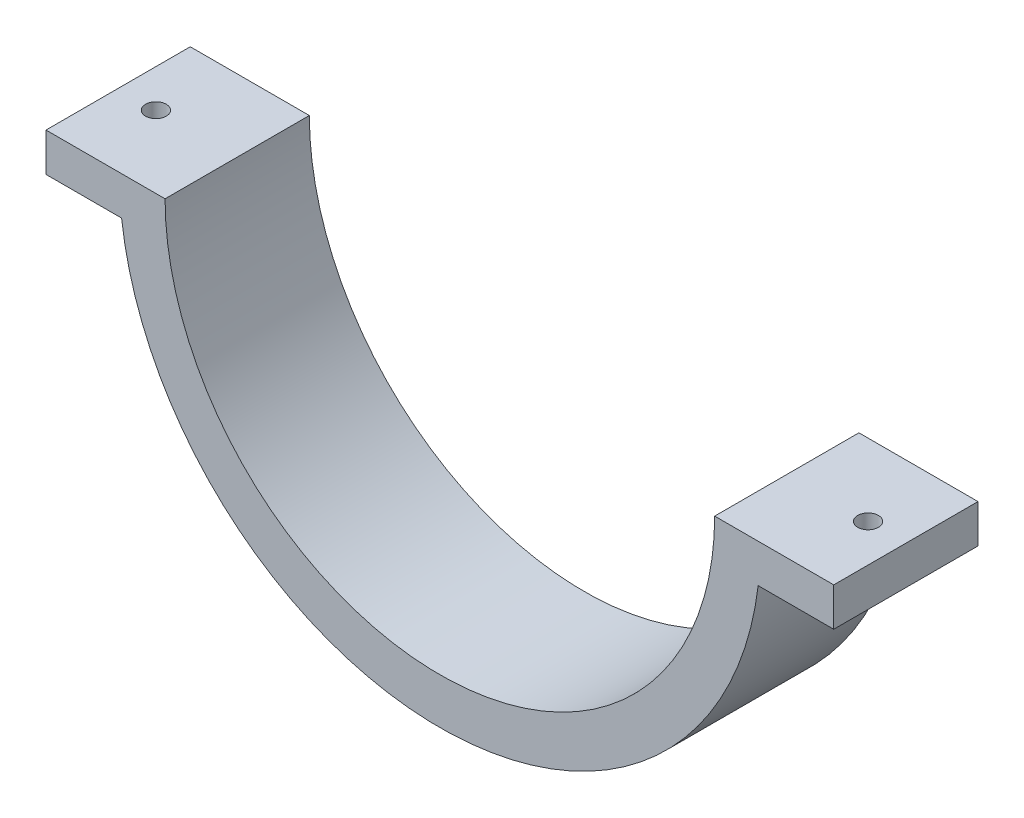
SolidWorks part; units mm, degrees
ref_plane "Front Plane" through (0, 0, 0) normal (0, 0, 1) x (1, 0, 0)
ref_plane "Top Plane" through (0, 0, 0) normal (0, 1, 0) x (1, 0, 0)
ref_plane "Right Plane" through (0, 0, 0) normal (1, 0, 0) x (0, 0, -1)
sketch "Sketch1" plane through (0, 0, 0) normal (0, 0, 1) x (1, 0, 0)
  line L0 (57.15, 0) -> (66.675, 0)
  line L1 (-66.675, 0) -> (-57.15, 0)
  circle A0 centre (0, 0) radius 57.15
  circle A1 centre (0, 0) radius 66.675
extrude "Boss-Extrude1" add sketch "Sketch1" along normal blind 30 contours L1 A1 L0 A0
sketch "Sketch2" plane through (0, 0, 30) normal (0, 0, 1) x (1, 0, 0)
  line L0 (57.15, 0) -> (66.675, 0) construction
  line L1 (61.9125, 0) -> (81.9125, 0)
  line L2 (61.9125, 0) -> (61.9125, -8)
  line L3 (61.9125, -8) -> (81.9125, -8)
  line L4 (81.9125, 0) -> (81.9125, -8)
  line L5 (-66.675, 0) -> (-57.15, 0) construction
  line L6 (-61.9125, 0) -> (-81.9125, 0)
  line L7 (-61.9125, 0) -> (-61.9125, -8)
  line L8 (-61.9125, -8) -> (-81.9125, -8)
  line L9 (-81.9125, 0) -> (-81.9125, -8)
  dimension "D1" = 8
  dimension "D2" = 8
  dimension "D3" = 20
  dimension "D4" = 20
extrude "Boss-Extrude2" add sketch "Sketch2" against normal blind 30
sketch "Sketch3" plane through (0, 0, 0) normal (0, 1, 0) x (1, 0, 0)
  line L0 (-81.9125, -15) -> (81.9125, -15) construction
  line L1 (-81.9125, 0) -> (-81.9125, -30) construction
  line L2 (81.9125, 0) -> (81.9125, -30) construction
  line L3 (-74.0529, -30) -> (-74.0529, 0) construction
  line L4 (-81.9125, -30) -> (-66.1933, -30) construction
  line L5 (-81.9125, 0) -> (-66.1933, 0) construction
  line L6 (0, 0) -> (0, -30) construction
  line L7 (-66.1933, -30) -> (66.1933, -30) construction
  circle A0 centre (-74.0529, -15) radius 2.1527
  circle A1 centre (74.0529, -15) radius 2.1527
extrude "Cut-Extrude1" cut sketch "Sketch3" against normal through all
